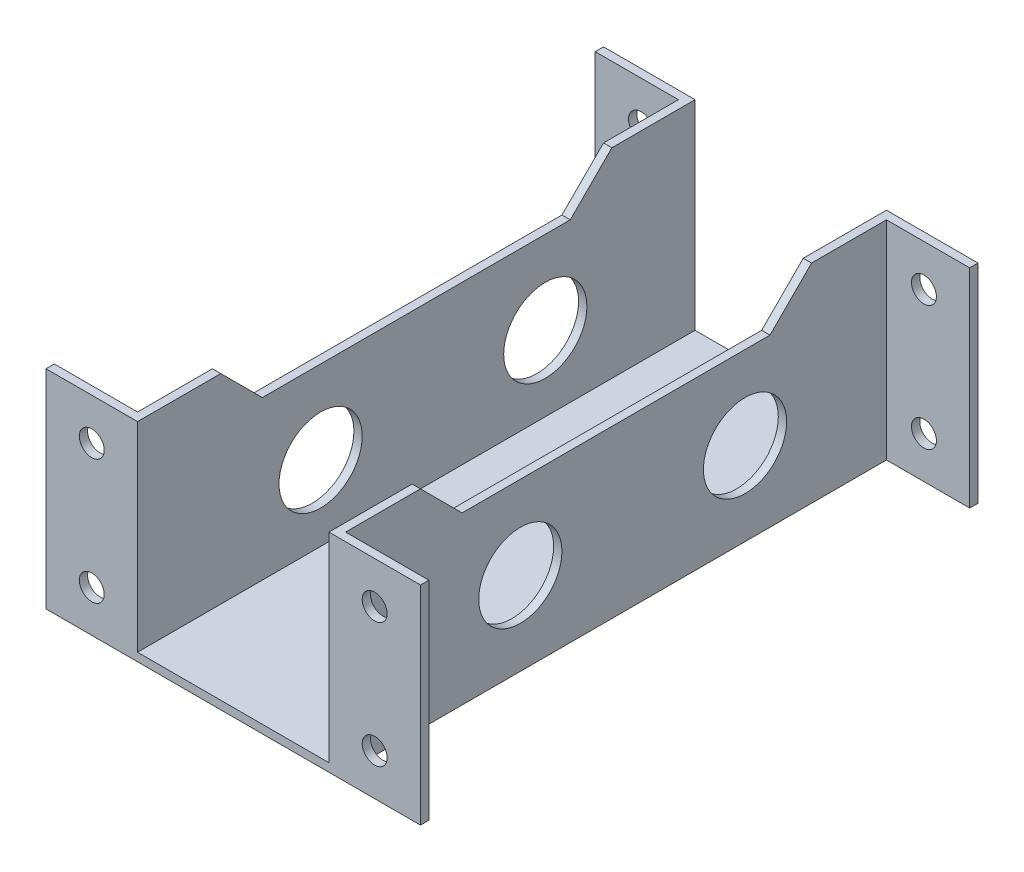
SolidWorks part; units mm, degrees
material "1060 Alloy"
ref_plane "Front Plane" through (0, 0, 0) normal (0, 0, 1) x (1, 0, 0)
ref_plane "Top Plane" through (0, 0, 0) normal (0, 1, 0) x (1, 0, 0)
ref_plane "Right Plane" through (0, 0, 0) normal (1, 0, 0) x (0, 0, -1)
sketch "Sketch1" plane through (0, 0, 0) normal (0, 1, 0) x (1, 0, 0)
  line L1 (-12.5, -33.5) -> (12.5, -33.5)
  line L2 (-12.5, -33.5) -> (-12.5, 33.5)
  line L3 (-12.5, 33.5) -> (12.5, 33.5)
  line L4 (12.5, -33.5) -> (12.5, 33.5)
  line L5 (-12.5, -33.5) -> (12.5, 33.5) construction
  line L6 (-12.5, 33.5) -> (12.5, -33.5) construction
  point P0 (0, 0)
  dimension "D1" = 67
  dimension "D2" = 25
extrude "Boss-Extrude1" add sketch "Sketch1" along normal blind 1
sketch "Sketch2" plane through (0, 1, 0) normal (0, 1, 0) x (1, 0, 0)
  line L0 (-12.5, -33.5) -> (12.5, -33.5) construction
  line L1 (12.5, 33.5) -> (11.5, 33.5)
  line L2 (12.5, 33.5) -> (12.5, -33.5)
  line L3 (12.5, -33.5) -> (11.5, -33.5)
  line L4 (11.5, 33.5) -> (11.5, -33.5)
  line L6 (-12.5, 33.5) -> (-11.5, 33.5)
  line L7 (-12.5, 33.5) -> (-12.5, -33.5)
  line L8 (-12.5, -33.5) -> (-11.5, -33.5)
  line L9 (-11.5, 33.5) -> (-11.5, -33.5)
  dimension "D1" = 1
  dimension "D2" = 1
extrude "Boss-Extrude2" add sketch "Sketch2" along normal blind 24
sketch "Sketch3" plane through (12.5, 0, 0) normal (1, 0, 0) x (0, 0, -1)
  line L0 (-33.5, 0) -> (33.5, 0) construction
  line L1 (-33.5, 25) -> (-32.5, 25)
  line L2 (-33.5, 25) -> (-33.5, 0)
  line L3 (-33.5, 0) -> (-32.5, 0)
  line L4 (-32.5, 25) -> (-32.5, 0)
  line L6 (33.5, 25) -> (32.5, 25)
  line L7 (33.5, 25) -> (33.5, 0)
  line L8 (33.5, 0) -> (32.5, 0)
  line L9 (32.5, 25) -> (32.5, 0)
  dimension "D1" = 1
  dimension "D2" = 1
extrude "Boss-Extrude3" add sketch "Sketch3" along normal blind 10
sketch "Sketch4" plane through (-12.5, 0, 0) normal (-1, 0, 0) x (0, 0, 1)
  line L0 (-33.5, 0) -> (33.5, 0) construction
  line L1 (-33.5, 25) -> (-32.5, 25)
  line L2 (-33.5, 25) -> (-33.5, 0)
  line L3 (-33.5, 0) -> (-32.5, 0)
  line L4 (-32.5, 25) -> (-32.5, 0)
  line L6 (33.5, 25) -> (32.5, 25)
  line L7 (33.5, 25) -> (33.5, 0)
  line L8 (33.5, 0) -> (32.5, 0)
  line L9 (32.5, 25) -> (32.5, 0)
  dimension "D1" = 1
  dimension "D2" = 1
extrude "Boss-Extrude4" add sketch "Sketch4" along normal blind 10
sketch "Sketch5" plane through (0, 1, 0) normal (0, 1, 0) x (1, 0, 0)
  line L0 (0, -33.5) -> (0, -16.5)
  line L1 (-11.5, -33.5) -> (11.5, -33.5) construction
  line L2 (0, -16.5) -> (0, -11.5)
  line L3 (0, -6.5) -> (0, 10.5)
  line L4 (0, 10.5) -> (0, 15.5)
  line L5 (0, 20.5) -> (0, 37.5)
  line L6 (0, 37.5) -> (0, 42.5)
  line L7 (0, 47.5) -> (0, 64.5)
  line L8 (0, 64.5) -> (0, 69.5)
  circle A0 centre (0, -11.5) radius 5
  circle A1 centre (0, 15.5) radius 5
  circle A2 centre (0, 42.5) radius 5
  circle A3 centre (0, 69.5) radius 5
  dimension "D1" = 17
  dimension "D2" = 5
  dimension "D3" = 17
  dimension "D4" = 5
  dimension "D5" = 17
  dimension "D6" = 5
  dimension "D7" = 17
  dimension "D8" = 5
extrude "Cut-Extrude1" cut sketch "Sketch5" against normal through all
sketch "Sketch10" plane through (0, 0, 33.5) normal (0, 0, 1) x (1, 0, 0)
  line L0 (17, 25) -> (17, 20)
  line L1 (11.5, 25) -> (22.5, 25) construction
  line L2 (17, 20) -> (22.5, 20)
  line L3 (22.5, 25) -> (22.5, 0) construction
  line L4 (17, 0) -> (17, 5)
  line L6 (-22.5, 0) -> (22.5, 0) construction
  line L7 (-17, 25) -> (-17, 20)
  line L8 (-22.5, 25) -> (-11.5, 25) construction
  circle A0 centre (17, 20) radius 1.5
  circle A1 centre (17, 5) radius 1.5
  circle A2 centre (-17, 20) radius 1.5
  circle A3 centre (-17, 5) radius 1.5
  dimension "D4" = 3
  dimension "D5" = 3
  dimension "D6" = 3
  dimension "D7" = 3
  dimension "D1" = 5
  dimension "D2" = 5
  dimension "D3" = 5
extrude "Cut-Extrude3" cut sketch "Sketch10" against normal through all
sketch "Sketch11" plane through (12.5, 0, 0) normal (1, 0, 0) x (0, 0, -1)
  line L0 (-33.5, 25) -> (-23.5, 25)
  line L1 (-32.5, 25) -> (32.5, 25) construction
  line L2 (-23.5, 25) -> (-18.5, 20)
  line L3 (-18.5, 20) -> (18.5, 20)
  line L4 (18.5, 20) -> (23.5, 25)
  line L5 (23.5, 25) -> (33.5, 25)
  line L6 (0, 25) -> (0, 20)
  line L7 (-23.5, 25) -> (23.5, 25)
  line M8 (32.5, 25) -> (-32.5, 25)
  dimension "D1" = 10
  dimension "D2" = 10
  dimension "D3" = 5
extrude "Cut-Extrude4" cut sketch "Sketch11" against normal through all and the other way through all contours L6 L2 L3 M8 | L6 L3 L4 M8
sketch "Sketch9" plane through (12.5, 0, 0) normal (1, 0, 0) x (0, 0, -1)
  line L0 (-21.4201, 0) -> (-21.4201, 10)
  line L2 (-16.5, 10) -> (-11.5, 10)
  line L3 (-6.5, 10) -> (10.5, 10)
  line L4 (10.5, 10) -> (15.5, 10)
  line L5 (20.5, 10) -> (37.5, 10)
  line L6 (37.5, 10) -> (42.5, 10)
  line L7 (47.5, 10) -> (64.5, 10)
  line L8 (64.5, 10) -> (69.5, 10)
  line L11 (-32.5, 0) -> (32.5, 0) construction
  line L12 (-16.5, 10) -> (-33.5, 10)
  line L14 (-33.5, 25) -> (-33.5, 0) construction
  circle A0 centre (-11.5, 10) radius 5
  circle A1 centre (15.5, 10) radius 5
  circle A2 centre (42.5, 10) radius 5
  circle A3 centre (69.5, 10) radius 5
  dimension "D1" = 10
  dimension "D2" = 5
  dimension "D3" = 17
  dimension "D4" = 5
  dimension "D5" = 17
  dimension "D6" = 5
  dimension "D7" = 17
  dimension "D8" = 5
  dimension "D9" = 17
extrude "Cut-Extrude2" cut sketch "Sketch9" against normal through all
